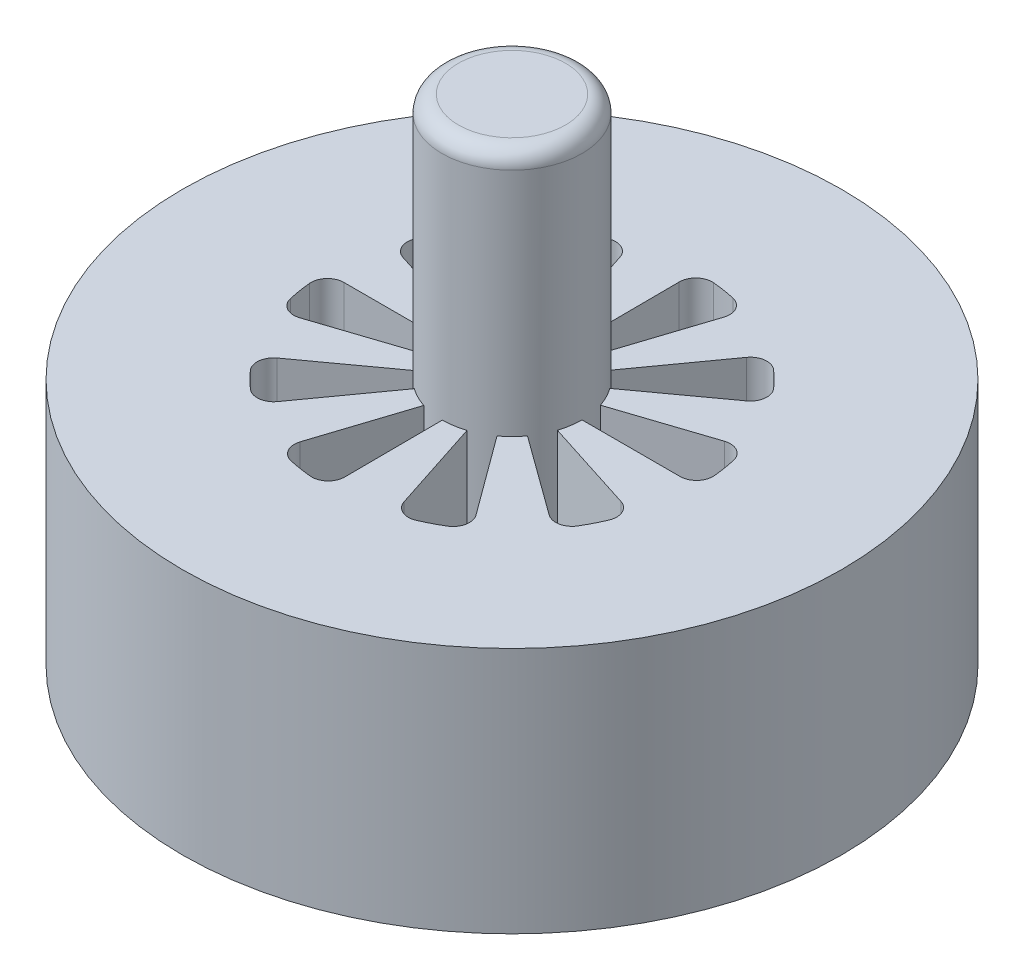
SolidWorks part; units mm, degrees
ref_plane "Front Plane" through (0, 0, 0) normal (0, 0, 1) x (1, 0, 0)
ref_plane "Top Plane" through (0, 0, 0) normal (0, 1, 0) x (1, 0, 0)
ref_plane "Right Plane" through (0, 0, 0) normal (1, 0, 0) x (0, 0, -1)
sketch "Sketch1" plane through (0, 0, 0) normal (0, 1, 0) x (1, 0, 0)
  line L0 (21.59, 0) -> (51.8216, 0)
  line L2 (20.4997, 6.7744) -> (49.2045, 16.2603)
  line L3 (20.5665, -6.5688) -> (49.3648, -15.7668)
  line L5 (57.15, 0) -> (21.59, 0)
  line L6 (17.4667, -12.6903) -> (41.9246, -30.46)
  line L7 (12.7776, -17.4029) -> (30.6695, -41.7715)
  line L8 (6.6717, -20.5333) -> (16.0138, -49.2853)
  line L9 (0.1081, -21.5897) -> (0.2594, -51.821)
  line L10 (-6.6717, -20.5333) -> (-16.0138, -49.2853)
  line L11 (-12.6027, -17.53) -> (-30.2497, -42.0765)
  line L12 (-17.4667, -12.6903) -> (-41.9246, -30.46)
  line L13 (-20.4997, -6.7744) -> (-49.2045, -16.2603)
  line L14 (-21.59, 0) -> (-51.8216, 0)
  line L15 (-20.5665, 6.5688) -> (-49.3648, 15.7668)
  line L16 (-17.4667, 12.6903) -> (-41.9246, 30.46)
  line L17 (-12.7776, 17.4029) -> (-30.6695, 41.7715)
  line L18 (-6.6717, 20.5333) -> (-16.0138, 49.2853)
  line L19 (-0.1081, 21.5897) -> (-0.2594, 51.821)
  line L20 (6.6717, 20.5333) -> (16.0138, 49.2853)
  line L21 (12.6027, 17.53) -> (30.2497, 42.0765)
  line L22 (17.4667, 12.6903) -> (41.9246, 30.46)
  circle A0 centre (0, 0) radius 101.6
  arc A1 (21.59, 0) -> (20.4997, 6.7744) centre (0, 0) ccw
  arc A2 (56.8774, 5.5756) -> (55.7544, 12.5526) centre (0, 0) ccw
  circle A3 centre (0, 0) radius 101.6
  arc A4 (49.292, -28.9209) -> (52.4845, -22.6163) centre (0, 0) ccw
  arc A5 (17.4667, -12.6903) -> (20.5665, -6.5688) centre (0, 0) ccw
  circle A6 centre (0, 0) radius 101.6
  arc A7 (22.8788, -52.3706) -> (29.1673, -49.1466) centre (0, 0) ccw
  arc A8 (6.6717, -20.5333) -> (12.7776, -17.4029) centre (0, 0) ccw
  circle A9 centre (0, 0) radius 101.6
  arc A10 (-12.2734, -55.8166) -> (-5.2908, -56.9046) centre (0, 0) ccw
  arc A11 (-6.6717, -20.5333) -> (0.1081, -21.5897) centre (0, 0) ccw
  circle A12 centre (0, 0) radius 101.6
  arc A13 (-42.7375, -37.9424) -> (-37.728, -42.9269) centre (0, 0) ccw
  arc A14 (-17.4667, -12.6903) -> (-12.6027, -17.53) centre (0, 0) ccw
  circle A15 centre (0, 0) radius 101.6
  arc A16 (-56.8774, -5.5756) -> (-55.7544, -12.5526) centre (0, 0) ccw
  arc A17 (-21.59, 0) -> (-20.4997, -6.7744) centre (0, 0) ccw
  circle A18 centre (0, 0) radius 101.6
  arc A19 (-49.292, 28.9209) -> (-52.4845, 22.6163) centre (0, 0) ccw
  arc A20 (-17.4667, 12.6903) -> (-20.5665, 6.5688) centre (0, 0) ccw
  circle A21 centre (0, 0) radius 101.6
  arc A22 (-22.8788, 52.3706) -> (-29.1673, 49.1466) centre (0, 0) ccw
  arc A23 (-6.6717, 20.5333) -> (-12.7776, 17.4029) centre (0, 0) ccw
  circle A24 centre (0, 0) radius 101.6
  arc A25 (12.2734, 55.8166) -> (5.2908, 56.9046) centre (0, 0) ccw
  arc A26 (6.6717, 20.5333) -> (-0.1081, 21.5897) centre (0, 0) ccw
  circle A27 centre (0, 0) radius 101.6
  arc A28 (42.7375, 37.9424) -> (37.728, 42.9269) centre (0, 0) ccw
  arc A29 (17.4667, 12.6903) -> (12.6027, 17.53) centre (0, 0) ccw
  arc A30 (-29.1673, 49.1466) -> (-30.6695, 41.7715) centre (-26.5747, 44.778) ccw
  arc A31 (-16.0138, 49.2853) -> (-22.8788, 52.3706) centre (-20.8451, 47.7155) ccw
  arc A32 (-49.292, 28.9209) -> (-41.9246, 30.46) centre (-44.9105, 26.3502) cw
  arc A33 (-52.4845, 22.6163) -> (-49.3648, 15.7668) centre (-47.8192, 20.606) ccw
  arc A34 (-56.8774, -5.5756) -> (-51.8216, 0) centre (-51.8216, -5.08) cw
  arc A35 (-55.7544, -12.5526) -> (-49.2045, -16.2603) centre (-50.7985, -11.4368) ccw
  arc A36 (-42.7375, -37.9424) -> (-41.9246, -30.46) centre (-38.9386, -34.5698) cw
  arc A37 (-37.728, -42.9269) -> (-30.2497, -42.0765) centre (-34.3744, -39.1112) ccw
  arc A38 (-5.2908, -56.9046) -> (0.2594, -51.821) centre (-4.8205, -51.8464) ccw
  arc A39 (-16.0138, -49.2853) -> (-12.2734, -55.8166) centre (-11.1824, -50.8551) ccw
  arc A40 (29.1673, -49.1466) -> (30.6695, -41.7715) centre (26.5747, -44.778) ccw
  arc A41 (22.8788, -52.3706) -> (16.0138, -49.2853) centre (20.8451, -47.7155) cw
  arc A42 (49.292, -28.9209) -> (41.9246, -30.46) centre (44.9105, -26.3502) cw
  arc A43 (52.4845, -22.6163) -> (49.3648, -15.7668) centre (47.8192, -20.606) ccw
  arc A44 (56.8774, 5.5756) -> (51.8216, 0) centre (51.8216, 5.08) cw
  arc A45 (55.7544, 12.5526) -> (49.2045, 16.2603) centre (50.7985, 11.4368) ccw
  arc A46 (42.7375, 37.9424) -> (41.9246, 30.46) centre (38.9386, 34.5698) cw
  arc A47 (37.728, 42.9269) -> (30.2497, 42.0765) centre (34.3744, 39.1112) ccw
  arc A48 (16.0138, 49.2853) -> (12.2734, 55.8166) centre (11.1824, 50.8551) ccw
  arc A49 (5.2908, 56.9046) -> (-0.2594, 51.821) centre (4.8205, 51.8464) ccw
  point P55 (0, 0)
  dimension "D1" = 203.2
  dimension "D2" = 43.18
  dimension "D3" = 114.3
  dimension "D5" = 5.08
  dimension "D4" = 10
extrude "Boss-Extrude1" add sketch "Sketch1" along normal blind 76.2 contours A8 L8 A7 L7 | A5 L6 A4 L3 | L0 A2 L2 A1 | A11 L10 A10 L9 | A14 L12 A13 L11 | A17 L14 A16 L13 | A20 L16 A19 L15 | A23 L18 A22 L17 | A26 L20 A25 L19 | A29 L22 A28 L21 | A0
sketch "Sketch2" plane through (0, 76.2, 0) normal (0, 1, 0) x (1, 0, 0)
  circle A0 centre (0, 0) radius 21.59
  point P3 (-240.7903, -30.9461)
extrude "Boss-Extrude2" add sketch "Sketch2" along normal blind 76.2
fillet "Fillet1" radius 5.08 1 edges at (0, 152.4, 21.59)
